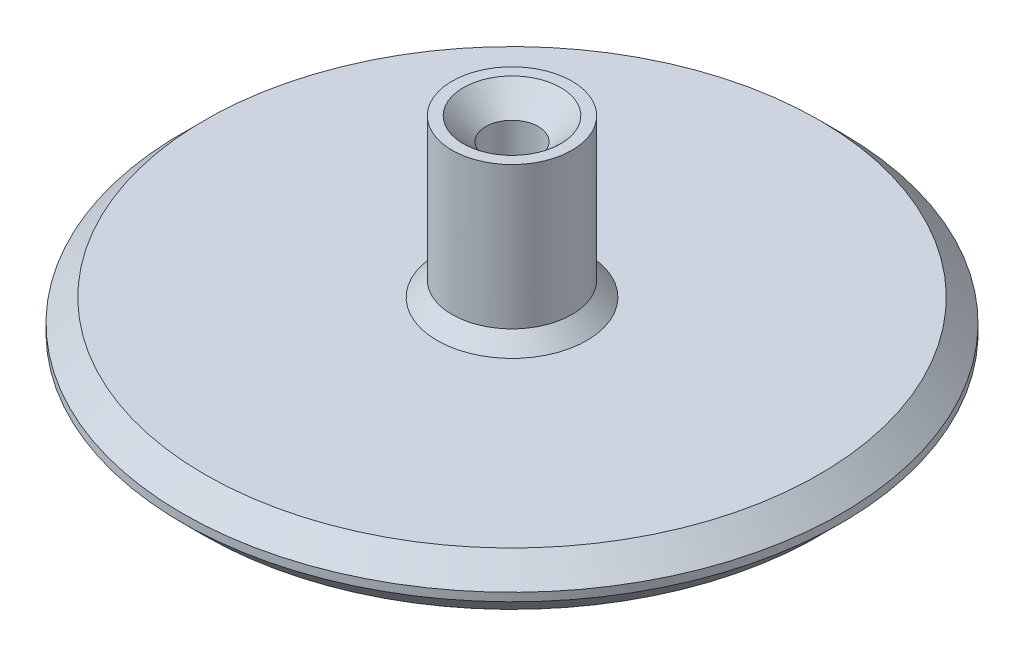
SolidWorks part; units mm, degrees
ref_plane "Front Plane" through (0, 0, 0) normal (0, 0, 1) x (1, 0, 0)
ref_plane "Top Plane" through (0, 0, 0) normal (0, 1, 0) x (1, 0, 0)
ref_plane "Right Plane" through (0, 0, 0) normal (1, 0, 0) x (0, 0, -1)
sketch "Sketch1" plane through (0, 0, 0) normal (0, 0, 1) x (1, 0, 0)
  line L0 (0, 0) -> (0, 24.495) construction
  line L2 (0, 0) -> (-20, 0)
  line L3 (0, 0) -> (0, 1.5)
  line L4 (0, 1.5) -> (-20, 1.5)
  line L5 (-20, 0) -> (-20, 1.5)
  line L6 (0, 0) -> (-20, 1.5) construction
  line L7 (0, 1.5) -> (-20, 0) construction
  line L8 (-20, 0) -> (-22, 0)
  line L9 (-20, 0) -> (-20, 3.55)
  line L10 (-20, 3.55) -> (-22, 3.55)
  line L11 (-22, 0) -> (-22, 3.55)
  line L12 (-20, 0) -> (-22, 3.55) construction
  line L13 (-20, 3.55) -> (-22, 0) construction
  line L14 (-20, 3.55) -> (-1.75, 3.55)
  line L15 (-20, 3.55) -> (-20, 2.05)
  line L16 (-20, 2.05) -> (-1.75, 2.05)
  line L17 (-1.75, 3.55) -> (-1.75, 2.05)
  line L18 (-20, 3.55) -> (-1.75, 2.05) construction
  line L19 (-20, 2.05) -> (-1.75, 3.55) construction
  line L20 (-1.75, 3.55) -> (-4, 3.55)
  line L21 (-1.75, 3.55) -> (-1.75, 14.05)
  line L22 (-1.75, 14.05) -> (-4, 14.05)
  line L23 (-4, 3.55) -> (-4, 14.05)
  line L24 (-1.75, 3.55) -> (-4, 14.05) construction
  line L25 (-1.75, 14.05) -> (-4, 3.55) construction
  point P6 (-10, 0.75)
  point P10 (-21, 1.775)
  point P14 (-10.875, 2.8)
  point P19 (-2.875, 8.8)
  dimension "D1" = 40
  dimension "D2" = 1.5
  dimension "D3" = 2
  dimension "D4" = 1.5
  dimension "D5" = 0.55
  dimension "D6" = 3.5
  dimension "D7" = 12
  dimension "D8" = 8
revolve "Revolve1" add sketch "Sketch1" angle 360 about L0
chamfer "Chamfer1" distance 1.5 angle 45 3 edges at (0, 0, -22) (0, 3.55, -22) (0, 14.05, -1.75)
chamfer "Chamfer2" distance 1 angle 45 1 edges at (0, 3.55, -4)
sketch "Sketch2" plane through (0, 0, 0) normal (0, -1, 0) x (1, 0, 0)
  line L0 (0, 0) -> (26.9446, 0) construction
  line L1 (1, -29.0344) -> (-1, -29.0344)
  line L2 (1, -29.0344) -> (1, 29.0344)
  line L3 (1, 29.0344) -> (-1, 29.0344)
  line L4 (-1, -29.0344) -> (-1, 29.0344)
  line L5 (1, -29.0344) -> (-1, 29.0344) construction
  line L6 (1, 29.0344) -> (-1, -29.0344) construction
  point P0 (0, 0)
  dimension "D1" = 2
  dimension "D2" = 58.0688
